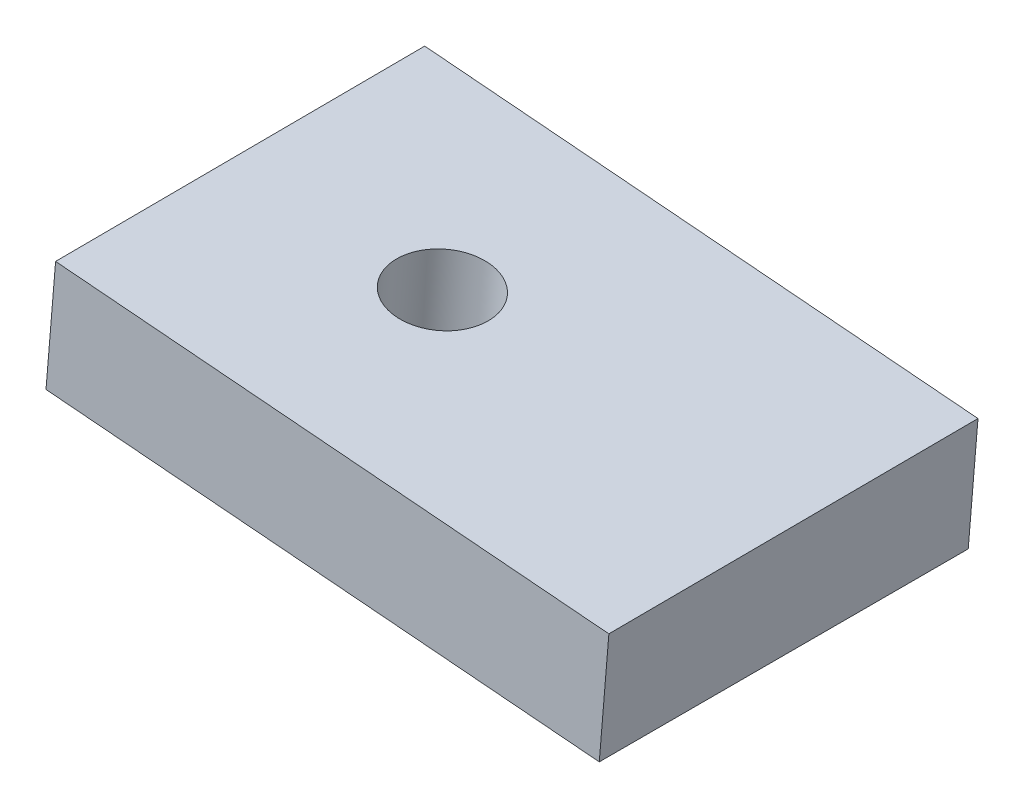
SolidWorks part; units mm, degrees
ref_plane "Front Plane" through (0, 0, 0) normal (0, 0, 1) x (1, 0, 0)
ref_plane "Top Plane" through (0, 0, 0) normal (0, 1, 0) x (1, 0, 0)
ref_plane "Right Plane" through (0, 0, 0) normal (1, 0, 0) x (0, 0, -1)
ref_plane "Plane1" through (-1.3154, -15.8621, 0) normal (-0.0826, -0.9966, 0) x (0.9966, -0.0826, 0)
sketch "Sketch1" plane through (-1.3154, -15.8621, 0) normal (-0.0826, -0.9966, 0) x (0.9966, -0.0826, 0)
  line L0 (-9.1777, 0) -> (-9.1777, 10)
  line L1 (-9.1777, 10) -> (-24.2253, 10)
  line L2 (-24.2253, 10) -> (-24.2253, 0)
  line L3 (-24.2253, 0) -> (-9.1777, 0)
extrude "Boss-Extrude1" add sketch "Sketch1" against normal blind 3.2038
draft "Draft1" type of draft neutral plane draft angle 0.326 faces to draft 1 face at (-17.6949, -11.289, 5) neutral plane through (-25.193, -10.6672, 0) neutral plane normal (0, 0, -1) reverse direction yes parameters "D1"=0.326
ref_plane "Plane2" through (-1.0524, -12.6904, 0) normal (0.0826, 0.9966, 0) x (0.9966, -0.0826, 0)
hole_wizard "#2 Clearance Hole1" positions "Sketch3" profile "Sketch2" hole size "#2" standard "ANSI Inch"
sketch "Sketch3" plane through (-1.0524, -12.6904, 0) normal (0.0826, 0.9966, 0) x (0.9966, -0.0826, 0)
  point P0 (-18.7253, -5)
sketch "Sketch2" plane through (-19.7136, -11.143, 5) normal (0, 0, 1) x (-0.9966, 0.0826, 0)
  line L0 (0, 0) -> (0, 4.4218)
  line L1 (0, 4.4218) -> (1.25, 4.4218)
  line L2 (1.25, 4.4218) -> (1.25, 0)
  line L5 (1.25, 0) -> (0, 0)
  line L11 (0, -6.35) -> (0, 107.95) construction
  dimension "Thru Hole Dia." = 2.5
  dimension "Thru Hole Depth" = 4.4218
